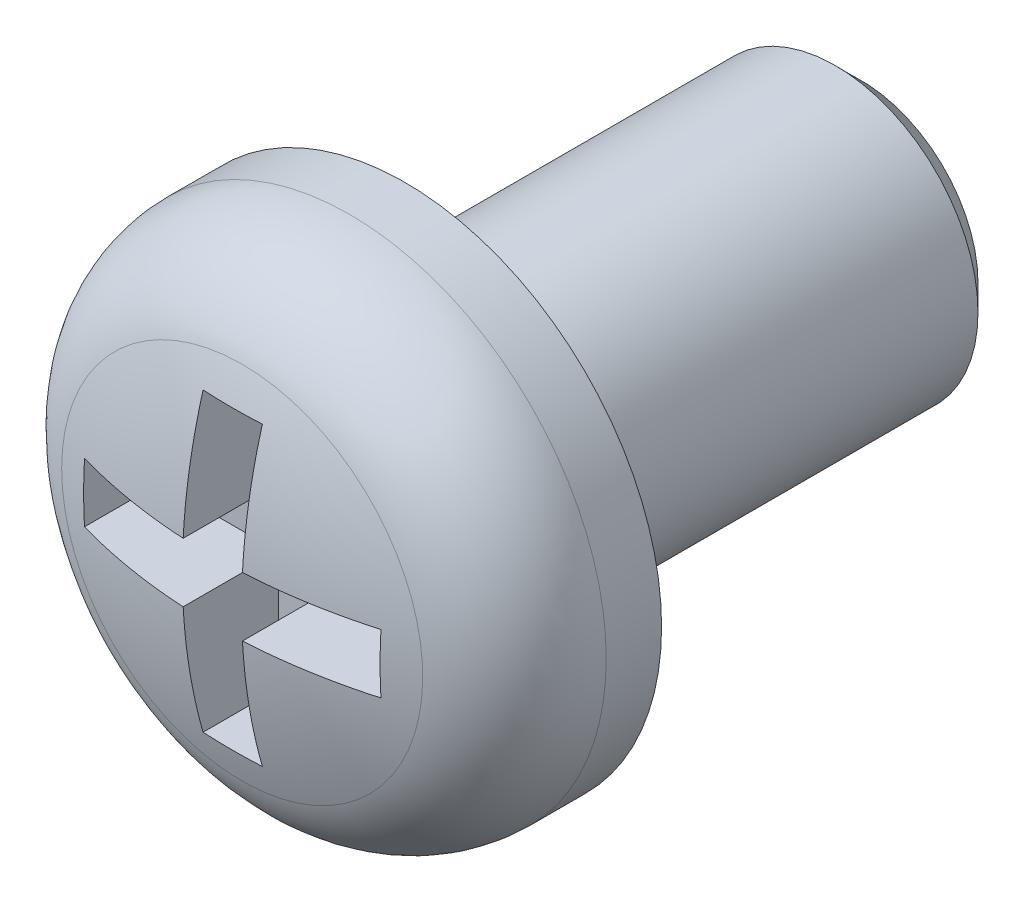
SolidWorks part; units mm, degrees
ref_plane "Front" through (0, 0, 0) normal (0, 0, 1) x (1, 0, 0)
ref_plane "Top" through (0, 0, 0) normal (0, 1, 0) x (1, 0, 0)
ref_plane "Right" through (0, 0, 0) normal (1, 0, 0) x (0, 0, -1)
sketch "Sketch1" plane through (0, 0, 0) normal (1, 0, 0) x (0, 0, -1)
  line L0 (-33.736, 0) -> (50.0028, 0) construction
  line L1 (-1.1333, 2.25) -> (0, 2.25)
  line L2 (0, 2.25) -> (0, 1.25)
  line L3 (0, 1.25) -> (4, 1.25)
  line L6 (4, 0) -> (-1.7, 0)
  line L8 (4, 1.25) -> (4, 0)
  arc A0 (-1.7, 0) -> (-1.1333, 2.25) centre (3.0502, 0) cw
  dimension "D1" = 2.5
  dimension "D2" = 1.1333
  dimension "l" = 4
  dimension "k+f" = 1.7
  dimension "dk" = 4.5
revolve "Revolve1" add sketch "Sketch1" angle 360 about L0
ref_plane "Plane1" through (0, 0, 1.7) normal (0, 0, -1) x (-1, 0, 0)
sketch "Sketch2" plane through (0, 0, 1.7) normal (0, 0, -1) x (-1, 0, 0)
  line L0 (0, 2.0016) -> (0, -1.8677) construction
  line L1 (2.0756, 0) -> (-1.9911, 0) construction
  line L2 (0, 1.3) -> (0.26, 1.3)
  line L3 (0.26, 1.3) -> (0.26, 0.26)
  line L4 (0.26, 0.26) -> (1.3, 0.26)
  line L5 (1.3, 0.26) -> (1.3, 0)
  line L6 (0.26, -1.3) -> (0, -1.3)
  line L7 (0.26, -0.26) -> (0.26, -1.3)
  line L8 (1.3, -0.26) -> (0.26, -0.26)
  line L9 (1.3, 0) -> (1.3, -0.26)
  line L10 (-1.3, -0.26) -> (-1.3, 0)
  line L11 (-0.26, -0.26) -> (-1.3, -0.26)
  line L12 (-0.26, -1.3) -> (-0.26, -0.26)
  line L13 (0, -1.3) -> (-0.26, -1.3)
  line L14 (-0.26, 1.3) -> (0, 1.3)
  line L15 (-0.26, 0.26) -> (-0.26, 1.3)
  line L16 (-1.3, 0.26) -> (-0.26, 0.26)
  line L17 (-1.3, 0) -> (-1.3, 0.26)
  dimension "D1" = 0.26
  dimension "m1/2" = 1.3
  dimension "D3" = 0.26
  dimension "m2/2" = 1.3
extrude "Cut-Extrude2" cut sketch "Sketch2" along normal blind 0.85
fillet "Fillet1" radius 1 1 edges at (2.25, 0, 1.1333)
chamfer "Chamfer1" distance 0.225 1 edges at (1.25, 0, -4)
equation "\"D1@Sketch2\" = \"m1/2@Sketch2\"/5"
equation "\"D3@Sketch2\" = \"m2/2@Sketch2\"/5"
equation "\"D1@Plane1\" = \"k+f@Sketch1\""
equation "\"D1@Cut-Extrude2\" = \"k+f@Sketch1\"/2"
equation "\"D2@Sketch1\" = \"k+f@Sketch1\"*2/3"
